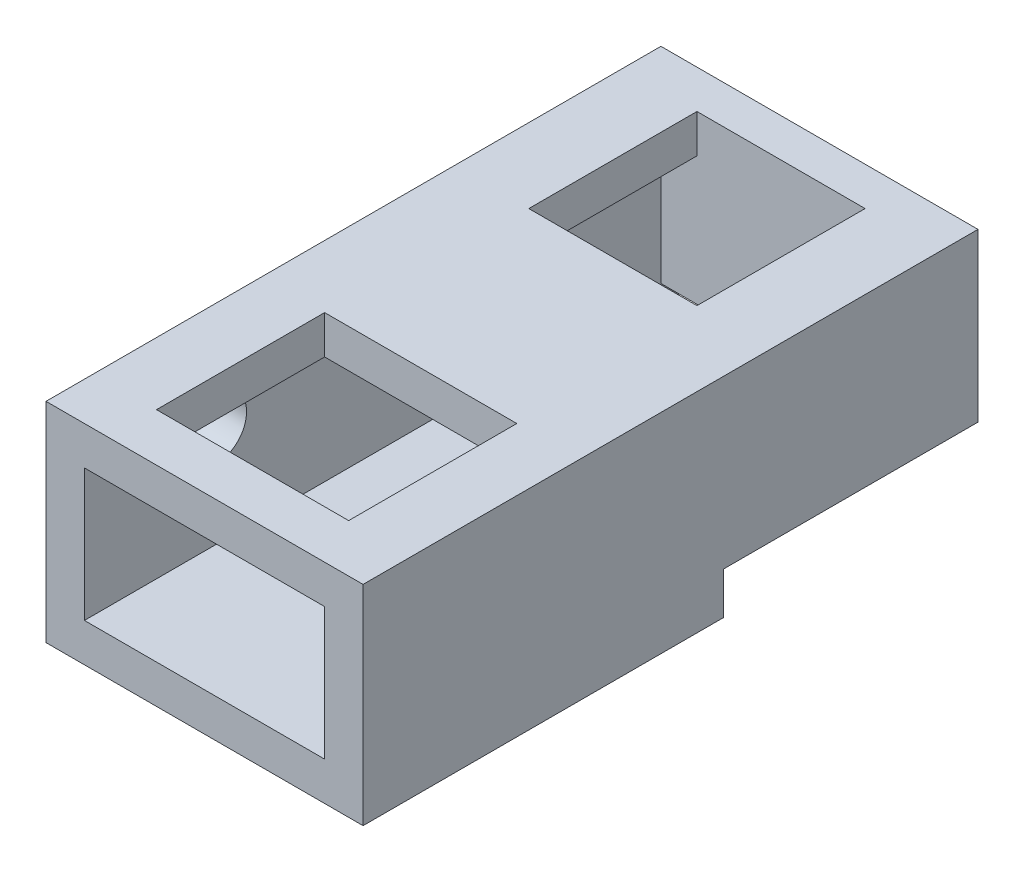
SolidWorks part; units mm, degrees
ref_plane "Front Plane" through (0, 0, 0) normal (0, 0, 1) x (1, 0, 0)
ref_plane "Top Plane" through (0, 0, 0) normal (0, 1, 0) x (1, 0, 0)
ref_plane "Right Plane" through (0, 0, 0) normal (1, 0, 0) x (0, 0, -1)
sketch "Sketch1" plane through (0, 0, 0) normal (0, 0, 1) x (1, 0, 0)
  line L1 (-116, 16) -> (-16, 16)
  line L2 (-116, 16) -> (-116, 71)
  line L3 (-116, 71) -> (-16, 71)
  line L4 (-16, 16) -> (-16, 71)
  line L7 (-132, 0) -> (0, 0)
  line L8 (-132, 0) -> (-132, 87)
  line L9 (-132, 87) -> (0, 87)
  line L10 (0, 0) -> (0, 87)
  point P0 (0, 0)
  point P6 (0, 0)
  point P11 (0, 0)
  dimension "D1" = 100
  dimension "D2" = 55
  dimension "D3" = 132
  dimension "D4" = 87
  dimension "D5" = 16
  dimension "D6" = 16
extrude "Boss-Extrude1" add sketch "Sketch1" along normal blind 256
sketch "Sketch4" plane through (0, 87, 0) normal (0, 1, 0) x (1, 0, 0)
  line L0 (0, -256) -> (-132, -256) construction
  line L6 (-106, -201) -> (-132, -201)
  line L7 (-106, -236) -> (-26, -236)
  line L8 (-106, -236) -> (-106, -166)
  line L9 (-106, -166) -> (-26, -166)
  line L10 (-26, -236) -> (-26, -166)
  line L11 (-132, -256) -> (-132, 0) construction
  line L12 (-26, -201) -> (0, -201)
  line L13 (0, -256) -> (0, 0) construction
  dimension "D1" = 80
  dimension "D2" = 70
  dimension "D3" = 20
extrude "Cut-Extrude1" cut sketch "Sketch4" against normal up to next contours L7 L10 L9 L8
sketch "Sketch5" plane through (0, 87, 0) normal (0, 1, 0) x (1, 0, 0)
  line L1 (-101, -16) -> (-31, -16)
  line L2 (-101, -16) -> (-101, -86)
  line L3 (-101, -86) -> (-31, -86)
  line L4 (-31, -16) -> (-31, -86)
  line L5 (0, 0) -> (-132, 0) construction
  line L6 (-132, -256) -> (-132, 0) construction
  dimension "D1" = 70
  dimension "D2" = 70
  dimension "D3" = 16
  dimension "D4" = 31
extrude "Cut-Extrude2" cut sketch "Sketch5" against normal up to next
sketch "Sketch6" plane through (0, 0, 0) normal (0, 0, -1) x (-1, 0, 0)
  line L1 (16, 71) -> (116, 71)
  line L2 (16, 71) -> (16, 16)
  line L3 (16, 16) -> (116, 16)
  line L4 (116, 71) -> (116, 16)
extrude "Boss-Extrude2" add sketch "Sketch6" against normal blind 16
sketch "Sketch7" plane through (0, 0, 0) normal (1, 0, 0) x (0, 0, -1)
  line L5 (0, 0) -> (-106, 0)
  line L6 (0, 0) -> (0, 17.5)
  line L7 (0, 17.5) -> (-106, 17.5)
  line L8 (-106, 0) -> (-106, 17.5)
  dimension "D1" = 17.5
  dimension "D2" = 106
extrude "Cut-Extrude3" cut sketch "Sketch7" against normal through all
sketch "Sketch9" plane through (-132, 0, 0) normal (-1, 0, 0) x (0, 0, 1)
  line L0 (106, 17.5) -> (106, 0) construction
  line L1 (0, 17.5) -> (106, 17.5)
  line L2 (0, 17.5) -> (0, 10)
  line L3 (0, 10) -> (106, 10)
  line L4 (106, 17.5) -> (106, 10)
  dimension "D1" = 7.5
extrude "Boss-Extrude4" add sketch "Sketch9" against normal blind 16
sketch "Sketch10" plane through (-132, 0, 0) normal (-1, 0, 0) x (0, 0, 1)
  line L0 (256, 87) -> (256, 0) construction
  line L1 (256, 0) -> (106, 0) construction
  circle A0 centre (201, 57.5) radius 12.5
  dimension "D1" = 25
  dimension "D2" = 55
  dimension "D3" = 57.5
extrude "Cut-Extrude4" cut sketch "Sketch10" against normal up to next
